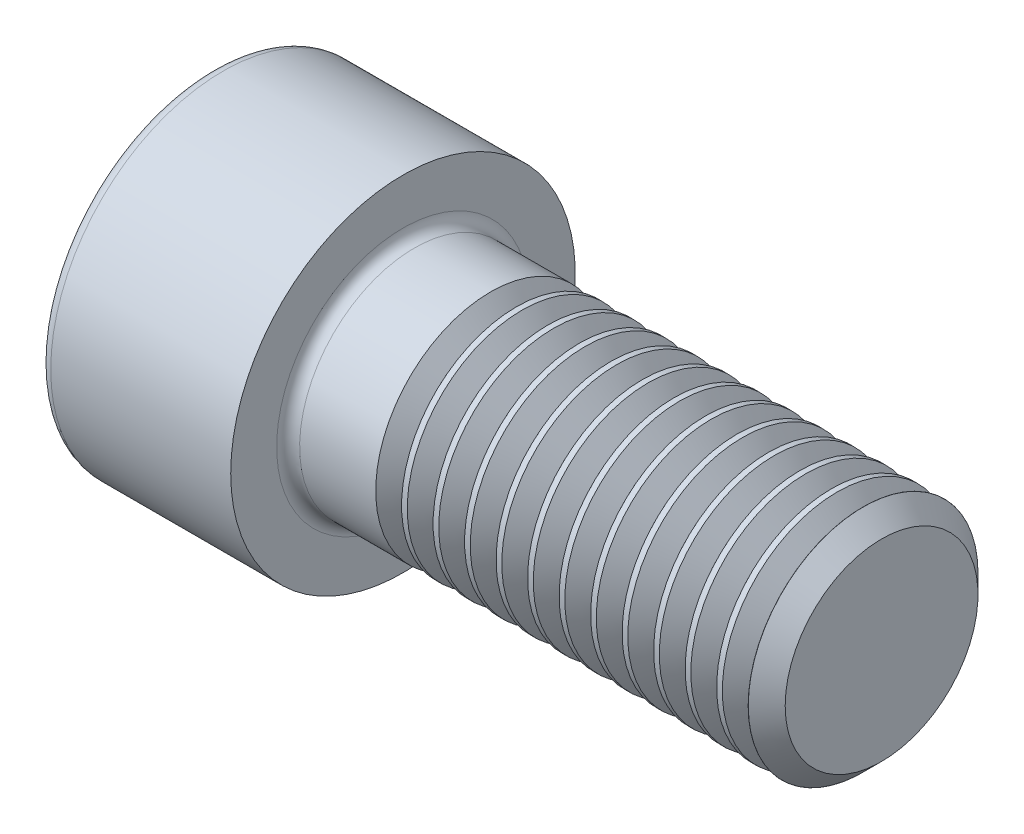
SolidWorks part; units mm, degrees
revolve "Base-Revolve" add sketch "BodySke"
sketch "BodySke" plane through (0, 0, 0) normal (0, 0, 1) x (1, 0, 0)
  line L0 (0, 0) -> (0, 9)
  line L1 (0, 9) -> (10, 9)
  line L2 (10, 9) -> (10, 6)
  line L3 (10, 6) -> (34.036, 6)
  line L4 (35, 5.036) -> (35, 0)
  line L5 (35, 0) -> (0, 0)
  line L6 (-31.75, 0) -> (127, 0) construction
  line L8 (35, 5.036) -> (34.036, 6)
  line L10 (35, -5.036) -> (34.036, -6) construction
  line L11 (11.75, 9.525) -> (11.75, 3.175) construction
  line L12 (10, 9.525) -> (10, 3.175) construction
  line L13 (-25, 9.525) -> (-25, 3.175) construction
  dimension "Head_ht" = 10
  dimension "Length" = 25
  dimension "Body_ch_ang" = 45
  dimension "Diameter" = 12
  dimension "Minor_dia" = 10.072
  dimension "Advance" = 1.75
  dimension "Thread_nom" = 25
  dimension "Thread_length" = 60
  dimension "Head_dia" = 18
cosmetic thread "ThreadCosmetic" [suppressed]
fillet "Fillet1" radius 0.6 1 edges at (10, 0, 6)
fillet "Fillet2" radius 0.6 1 edges at (0, 0, 9)
ref_plane "Plane1" through (0, 0, 0) normal (0, 0, 1) x (1, 0, 0)
ref_plane "Plane2" through (0, 0, 0) normal (0, 1, 0) x (1, 0, 0)
ref_plane "Plane3" through (0, 0, 0) normal (1, 0, 0) x (0, 0, -1)
other "Configuration Table"
sketch "Sketch2" plane through (0, 0, 0) normal (0, 0, 1) x (1, 0, 0)
  line L0 (0, 5.0575) -> (6, 5.0575)
  line L1 (6, 5.0575) -> (8.9199, 0)
  line L2 (-31.75, 0) -> (127, 0) construction
  line L3 (8.9199, 0) -> (0, 0)
  line L4 (0, 0) -> (0, 5.0575)
  line L6 (0, 0) -> (47.625, 0) construction
  dimension "D1" = 5.0575
  dimension "D2" = 60
  dimension "Depth" = 6
revolve "Hex-PreBroach" cut sketch "Sketch2" angle 360 about L6
sketch "Sketch3" plane through (0, 0, 0) normal (-1, 0, 0) x (0, 0.5, 0.866)
  line L0 (2.9199, 5.0575) -> (-2.9199, 5.0575)
  line L1 (-2.9199, 5.0575) -> (-5.8399, 0)
  line L2 (2.9199, 5.0575) -> (5.8399, 0)
  line L3 (2.9199, -5.0575) -> (5.8399, 0)
  line L4 (2.9199, -5.0575) -> (-2.9199, -5.0575)
  line L5 (-2.9199, -5.0575) -> (-5.8399, 0)
  dimension "D1" = 5.0575
  dimension "D2" = 5.0575
  dimension "Hex_size" = 10.115
extrude "Hex" cut sketch "Sketch3" against normal blind 6
sketch "ThdSchSke" plane through (0, 0, 0) normal (0, 0, 1) x (1, 0, 0)
  line L0 (15.25, -5.036) -> (14.575, -6)
  line L1 (15.25, -5.036) -> (15.925, -6)
  line L2 (15.925, -6) -> (15.925, -7.5)
  line L3 (-3.175, 0) -> (5.1513, 0) construction
  line L4 (0, 8.4) -> (0, -8.4) construction
  line L5 (15.925, -7.5) -> (14.575, -7.5)
  line L6 (14.575, -7.5) -> (14.575, -6)
  dimension "Thread_minor" = 10.072
  dimension "Diameter" = 12
  dimension "Start" = 15.25
revolve "ThreadSchematic" cut sketch "ThdSchSke" angle 360 about L3
pattern_linear "ThdSchPat" count 12 spacing 1.6458 along (1, 0, 0) of "ThreadSchematic"
equation "\"D2@Sketch3\" = \"Hex_size@Sketch3\" / 2"
equation "\"D1@Sketch3\" = \"Hex_size@Sketch3\" / 2"
equation "\"D1@Sketch2\" = \"Hex_size@Sketch3\" / 2"
equation "\"Thread_minor@ThreadCosmetic\"  =  \"Minor_dia@BodySke\""
equation "\"Depth@Sketch2\" =  \"Key_eng@Hex\""
equation "\"Thread_length@ThreadCosmetic\" = ((sgn( (\"Length@BodySke\" - \"Advance@BodySke\" * 3.0) - \"Thread_nom@BodySke\" )-1)*( (\"Length@BodySke\" - \"Advance@BodySke\" * 3.0) - \"Thread_nom@BodySke\" ))/-2+ \"Thread_nom@BodySke\""
equation "\"Thread_minor@ThdSchSke\" = \"Minor_dia@BodySke\""
equation "\"Diameter@ThdSchSke\" = \"Diameter@BodySke\""
equation "\"Overcut@ThdSchSke\" = \"Diameter@BodySke\" * 1.25"
equation "\"Start@ThdSchSke\" = \"Head_ht@BodySke\" + \"Length@BodySke\" - \"Thread_length@ThreadCosmetic\"  '---Non-countersunk---"
equation "\"Num_threads@ThdSchPat\" = int( \"Thread_length@ThreadCosmetic\" / \"Advance@BodySke\" + 0.999 )  + 1"
equation "\"Advance@ThdSchPat\" = \"Thread_length@ThreadCosmetic\" /  (\"Num_threads@ThdSchPat\" - 1) 'relax it"
equation "\"Num_threads@ThdSchPat\" = \"Num_threads@ThdSchPat\" - sgn( \"Num_threads@ThdSchPat\" - 1) '---chamfered tips only---"
